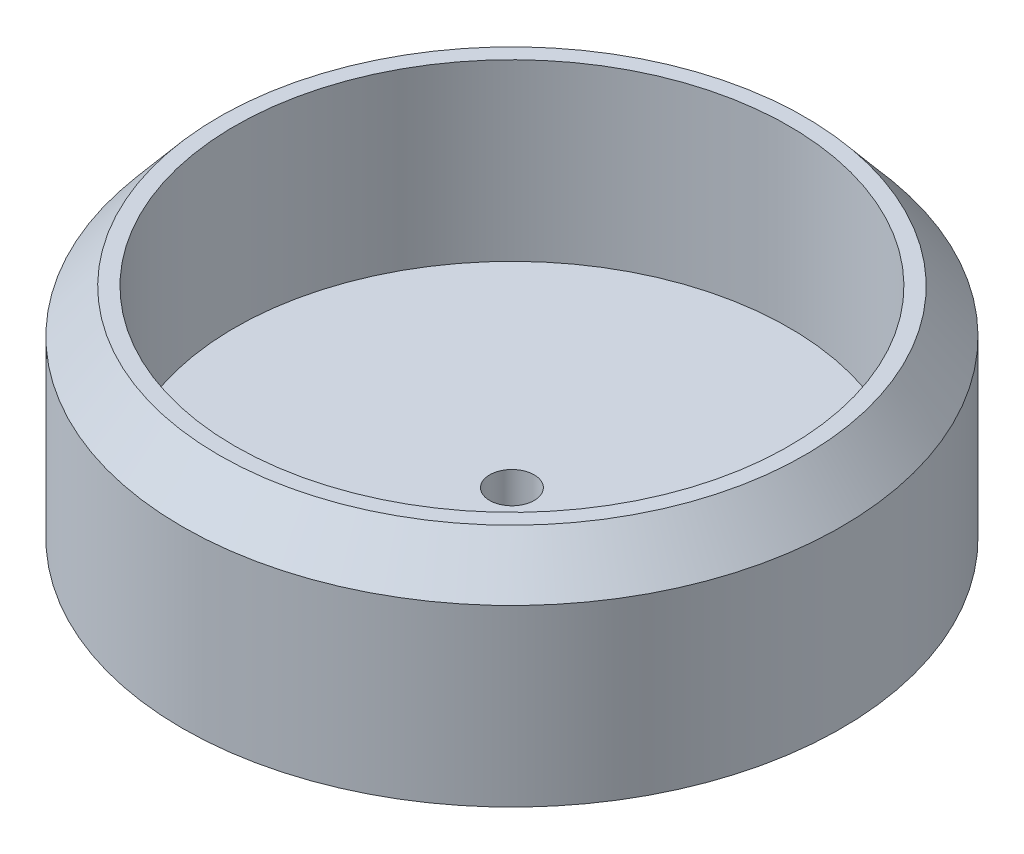
SolidWorks part; units mm, degrees
material "PVC Rigid"
ref_plane "Front Plane" through (0, 0, 0) normal (0, 0, 1) x (1, 0, 0)
ref_plane "Top Plane" through (0, 0, 0) normal (0, 1, 0) x (1, 0, 0)
ref_plane "Right Plane" through (0, 0, 0) normal (1, 0, 0) x (0, 0, -1)
sketch "Sketch1" plane through (0, 0, 0) normal (0, 1, 0) x (1, 0, 0)
  circle A0 centre (0, 0) radius 37.75
  dimension "D1" = 75.5
extrude "Boss-Extrude1" add sketch "Sketch1" along normal blind 5
sketch "Sketch2" plane through (0, 5, 0) normal (0, 1, 0) x (1, 0, 0)
  circle A0 centre (0, 0) radius 31.7505
  circle A1 centre (0, 0) radius 37.75 construction
  circle A2 centre (0, 0) radius 37.75
  dimension "D1" = 63.501
extrude "Boss-Extrude2" add sketch "Sketch2" along normal blind 20
chamfer "Chamfer1" distance 5 angle 40 1 edges at (0, 25, 37.75)
sketch "Sketch3" plane through (0, 0, 0) normal (0, -1, 0) x (1, 0, 0)
  circle A0 centre (0, 0) radius 2.55
  dimension "D1" = 5.1
extrude "Cut-Extrude1" cut sketch "Sketch3" against normal through all and the other way through all
